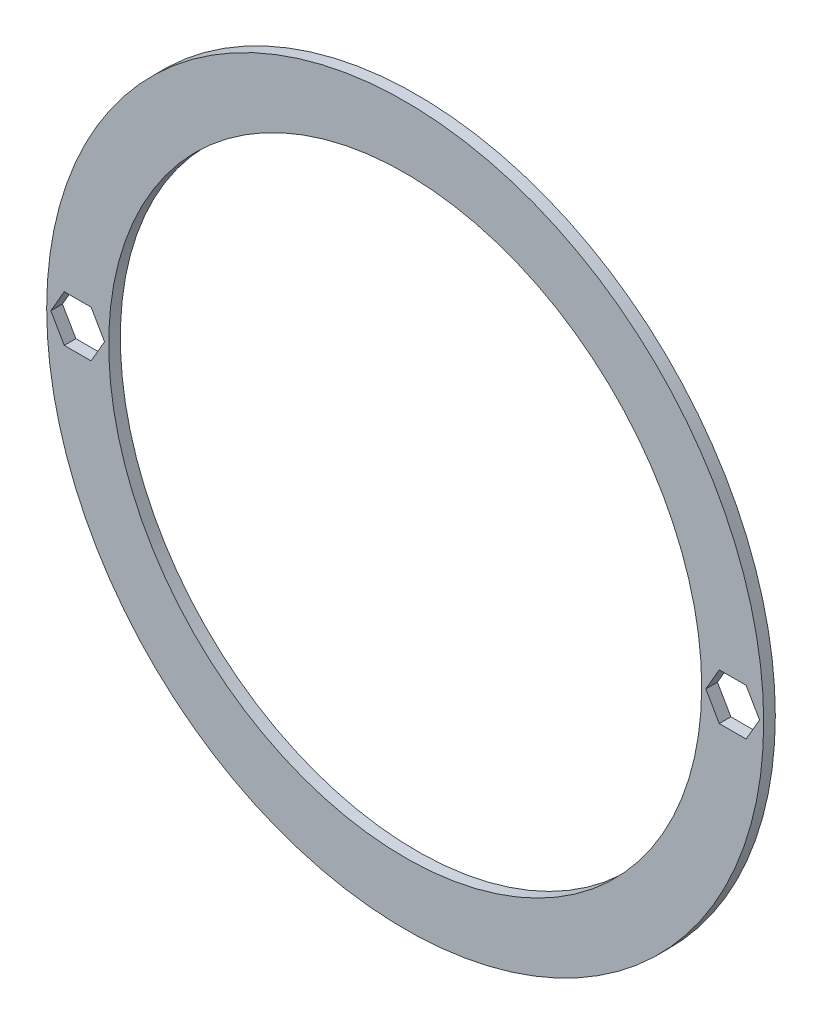
SolidWorks part; units mm, degrees
ref_plane "Plan de face" through (0, 0, 0) normal (0, 0, 1) x (1, 0, 0)
ref_plane "Plan de dessus" through (0, 0, 0) normal (0, 1, 0) x (1, 0, 0)
ref_plane "Plan de droite" through (0, 0, 0) normal (1, 0, 0) x (0, 0, -1)
sketch "Esquisse1" plane through (0, 0, 0) normal (0, 0, 1) x (1, 0, 0)
  line L0 (-46.25, 0) -> (-42.25, 0) construction
  line L1 (-40.5179, 3) -> (-43.9821, 3)
  line L2 (-43.9821, 3) -> (-45.7141, 0)
  line L3 (-45.7141, 0) -> (-43.9821, -3)
  line L4 (-43.9821, -3) -> (-40.5179, -3)
  line L5 (-40.5179, -3) -> (-38.7859, 0)
  line L6 (-38.7859, 0) -> (-40.5179, 3)
  line L13 (-42.25, 0) -> (-38.25, 0) construction
  line L14 (0, 0) -> (0, 38.25) construction
  line L15 (38.7859, 0) -> (40.5179, 3)
  line L16 (40.5179, -3) -> (38.7859, 0)
  line L17 (43.9821, -3) -> (40.5179, -3)
  line L18 (45.7141, 0) -> (43.9821, -3)
  line L19 (43.9821, 3) -> (45.7141, 0)
  line L20 (40.5179, 3) -> (43.9821, 3)
  circle A0 centre (0, 0) radius 46.25
  circle A1 centre (0, 0) radius 38.25
  circle A2 centre (-42.25, 0) radius 3 construction
  dimension "D1" = 92.5
  dimension "D3" = 6
  dimension "D2" = 8
extrude "Boss.-Extru.1" add sketch "Esquisse1" along normal blind 1.5
